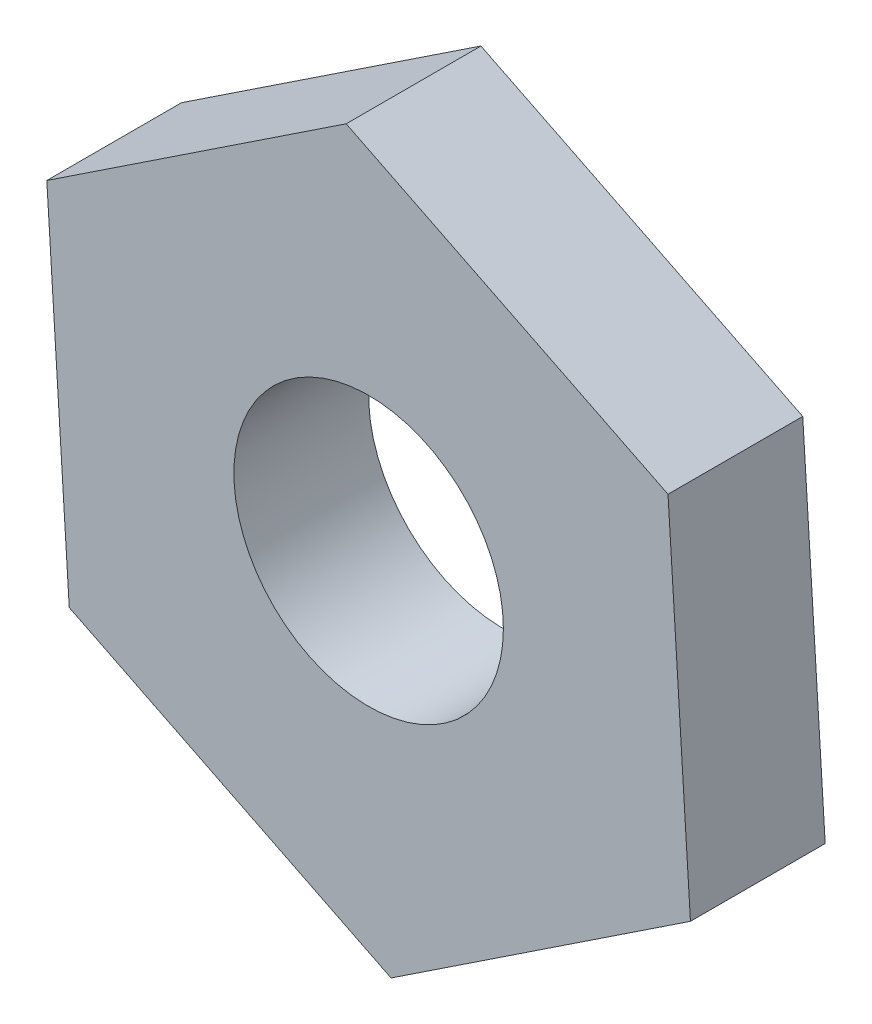
SolidWorks part; units mm, degrees
ref_plane "Front Plane" through (0, 0, 0) normal (0, 0, 1) x (1, 0, 0)
ref_plane "Top Plane" through (0, 0, 0) normal (0, 1, 0) x (1, 0, 0)
ref_plane "Right Plane" through (0, 0, 0) normal (1, 0, 0) x (0, 0, -1)
sketch "Sketch1" plane through (0, 0, 0) normal (0, 0, 1) x (1, 0, 0)
  line L1 (-3.3324, -2.2125) -> (0.2499, -3.9922)
  line L2 (0.2499, -3.9922) -> (3.5823, -1.7797)
  line L3 (3.5823, -1.7797) -> (3.3324, 2.2125)
  line L4 (3.3324, 2.2125) -> (-0.2499, 3.9922)
  line L5 (-0.2499, 3.9922) -> (-3.5823, 1.7797)
  line L6 (-3.5823, 1.7797) -> (-3.3324, -2.2125)
  circle A0 centre (0, 0) radius 3.4641 construction
  dimension "D1" = 4
extrude "Boss-Extrude1" add sketch "Sketch1" along normal blind 1.5
sketch "Sketch2" plane through (0, 0, 1.5) normal (0, 0, 1) x (1, 0, 0)
  circle A0 centre (0, 0) radius 1.5
  dimension "D1" = 3
extrude "Cut-Extrude1" cut sketch "Sketch2" against normal through all
